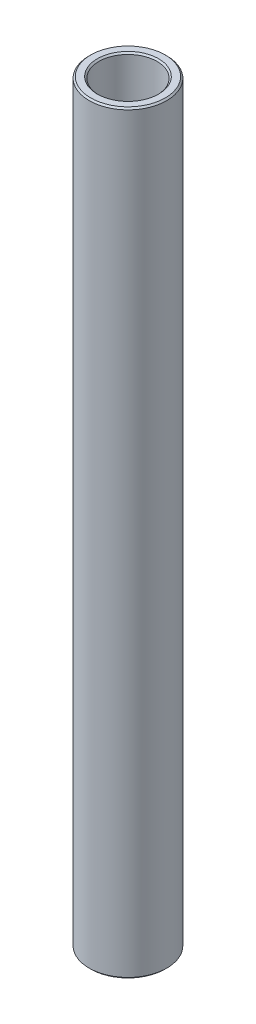
SolidWorks part; units mm, degrees
ref_plane "Front Plane" through (0, 0, 0) normal (0, 0, 1) x (1, 0, 0)
ref_plane "Top Plane" through (0, 0, 0) normal (0, 1, 0) x (1, 0, 0)
ref_plane "Right Plane" through (0, 0, 0) normal (1, 0, 0) x (0, 0, -1)
sketch "Sketch1" plane through (0, 0, 0) normal (0, 0, 1) x (1, 0, 0)
  line L0 (0, 11.6086) -> (0, -11.6086) construction
  line L1 (4.7625, 61.7163) -> (6.35, 61.7163)
  line L2 (6.35, 61.7163) -> (6.35, -61.7163)
  line L3 (6.35, -61.7163) -> (4.7625, -61.7163)
  line L4 (4.7625, -61.7163) -> (4.7625, 61.7163)
  line L5 (4.7625, 0) -> (0, 0) construction
  dimension "D1" = 9.525
  dimension "D2" = 12.7
  dimension "D3" = 123.4326
revolve "Revolve1" add sketch "Sketch1" angle 360 about L0
chamfer "Chamfer1" distance 0.254 angle 45 4 edges at (-4.7625, -61.7163, 0) (-6.35, -61.7163, 0) (-6.35, 61.7163, 0) (-4.7625, 61.7163, 0)
